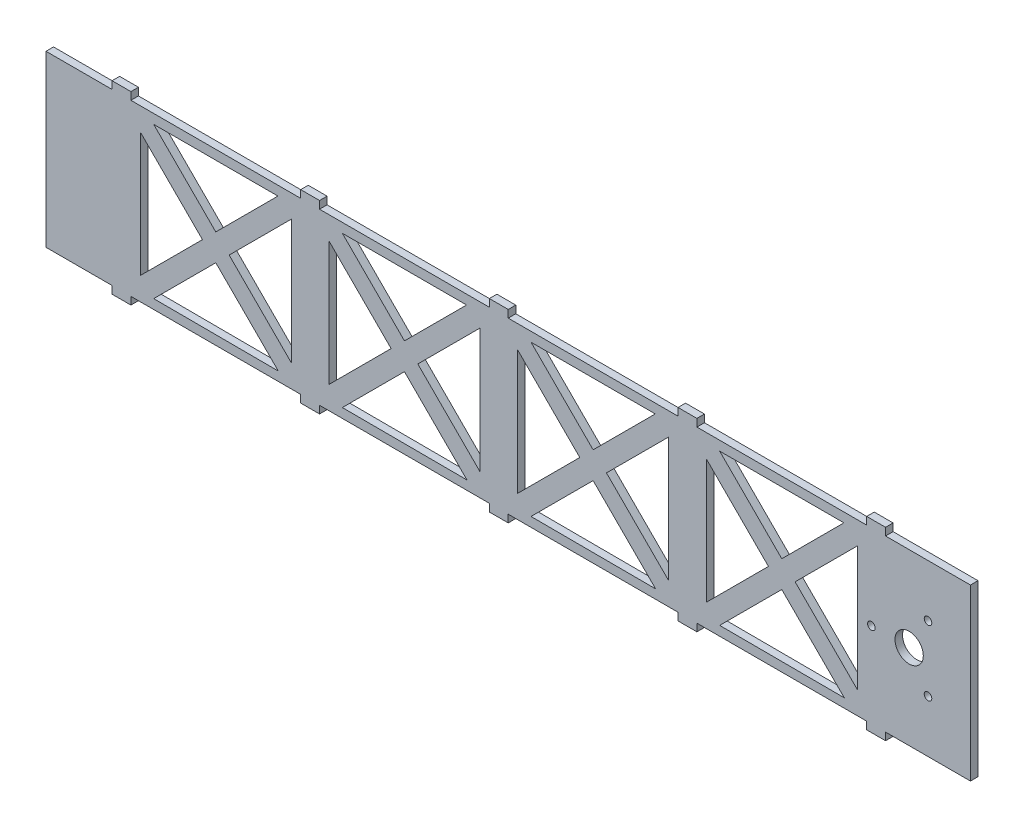
SolidWorks part; units mm, degrees
ref_plane "Piano frontale" through (0, 0, 0) normal (0, 0, 1) x (1, 0, 0)
ref_plane "Piano superiore" through (0, 0, 0) normal (0, 1, 0) x (1, 0, 0)
ref_plane "Piano destro" through (0, 0, 0) normal (1, 0, 0) x (0, 0, -1)
sketch "Schizzo1" plane through (0, 0, 0) normal (0, 0, 1) x (1, 0, 0)
  line L0 (0, 90) -> (0, 0)
  line L1 (0, 0) -> (35, 0)
  line L3 (0, 90) -> (35, 90)
  line L4 (490, 0) -> (490, 90)
  line L6 (490, 45) -> (0, 45) construction
  line L9 (45, 90) -> (45, 0) construction
  line L10 (135, 90) -> (135, 0) construction
  line L11 (45, 90) -> (135, 0) construction
  line L12 (45, 0) -> (135, 0) construction
  line L13 (135, 90) -> (45, 0) construction
  line L14 (50, 77.9289) -> (50, 12.0711)
  line L15 (130, 77.9289) -> (130, 12.0711)
  line L16 (45, 0) -> (50, 0) construction
  line L17 (50, 77.9289) -> (82.9289, 45)
  line L18 (57.0711, 85) -> (90, 52.0711)
  line L19 (122.9289, 85) -> (90, 52.0711)
  line L20 (130, 77.9289) -> (97.0711, 45)
  line L21 (57.0711, 85) -> (122.9289, 85)
  line L22 (123.1448, 4.7841) -> (57.0772, 5.0061)
  line L23 (131.4645, 93.5355) -> (41.4645, 3.5355) construction
  line L24 (138.5355, 86.4645) -> (48.5355, -3.5355) construction
  line L26 (41.4645, 86.4645) -> (131.4645, -3.5355) construction
  line L27 (130, 90) -> (130, 0) construction
  line L28 (48.5355, 93.5355) -> (138.5355, 3.5355) construction
  line L29 (90, 37.9289) -> (123.1448, 4.7841)
  line L30 (97.0711, 45) -> (130, 12.0711)
  line L31 (82.9289, 45) -> (50, 12.0711)
  line L32 (90, 37.9289) -> (57.0772, 5.0061)
  line L33 (150, 77.9289) -> (150, 12.0711)
  line L34 (230, 77.9289) -> (230, 12.0711)
  line L35 (150, 77.9289) -> (182.9289, 45)
  line L36 (157.0711, 85) -> (190, 52.0711)
  line L37 (222.9289, 85) -> (190, 52.0711)
  line L38 (230, 77.9289) -> (197.0711, 45)
  line L39 (157.0711, 85) -> (222.9289, 85)
  line L40 (223.1448, 4.7841) -> (157.0772, 5.0061)
  line L41 (190, 37.9289) -> (223.1448, 4.7841)
  line L42 (197.0711, 45) -> (230, 12.0711)
  line L43 (182.9289, 45) -> (150, 12.0711)
  line L44 (190, 37.9289) -> (157.0772, 5.0061)
  line L45 (445, 94) -> (445, 90)
  line L46 (250, 77.9289) -> (250, 12.0711)
  line L47 (330, 77.9289) -> (330, 12.0711)
  line L48 (250, 77.9289) -> (282.9289, 45)
  line L49 (257.0711, 85) -> (290, 52.0711)
  line L50 (322.9289, 85) -> (290, 52.0711)
  line L51 (330, 77.9289) -> (297.0711, 45)
  line L52 (257.0711, 85) -> (322.9289, 85)
  line L53 (323.1448, 4.7841) -> (257.0772, 5.0061)
  line L54 (290, 37.9289) -> (323.1448, 4.7841)
  line L55 (297.0711, 45) -> (330, 12.0711)
  line L56 (282.9289, 45) -> (250, 12.0711)
  line L57 (290, 37.9289) -> (257.0772, 5.0061)
  line L58 (350, 77.9289) -> (350, 12.0711)
  line L59 (430, 77.9289) -> (430, 12.0711)
  line L60 (350, 77.9289) -> (382.9289, 45)
  line L61 (357.0711, 85) -> (390, 52.0711)
  line L62 (422.9289, 85) -> (390, 52.0711)
  line L63 (430, 77.9289) -> (397.0711, 45)
  line L64 (435, 94) -> (445, 94)
  line L65 (357.0711, 85) -> (422.9289, 85)
  line L66 (423.1448, 4.7841) -> (357.0772, 5.0061)
  line L67 (390, 37.9289) -> (423.1448, 4.7841)
  line L68 (397.0711, 45) -> (430, 12.0711)
  line L69 (382.9289, 45) -> (350, 12.0711)
  line L70 (390, 37.9289) -> (357.0772, 5.0061)
  line L71 (50, 77.9289) -> (150, 77.9289) construction
  line L83 (435, 90) -> (435, 94)
  line L85 (35, 0) -> (35, -4)
  line L86 (35, -4) -> (45, -4)
  line L87 (45, -4) -> (45, 0)
  line L88 (135, 0) -> (135, -4)
  line L89 (135, -4) -> (145, -4)
  line L90 (145, -4) -> (145, 0)
  line L91 (235, 0) -> (235, -4)
  line L92 (235, -4) -> (245, -4)
  line L93 (245, -4) -> (245, 0)
  line L94 (335, 0) -> (335, -4)
  line L95 (335, -4) -> (345, -4)
  line L96 (345, -4) -> (345, 0)
  line L97 (435, 0) -> (435, -4)
  line L98 (435, -4) -> (445, -4)
  line L99 (445, -4) -> (445, 0)
  line L100 (445, 0) -> (490, 0)
  line L101 (345, 0) -> (435, 0)
  line L102 (245, 0) -> (335, 0)
  line L103 (145, 0) -> (235, 0)
  line L104 (45, 0) -> (135, 0)
  line L108 (345, 94) -> (345, 90)
  line L109 (335, 94) -> (345, 94)
  line L110 (335, 90) -> (335, 94)
  line L111 (245, 94) -> (245, 90)
  line L112 (235, 94) -> (245, 94)
  line L113 (235, 90) -> (235, 94)
  line L114 (145, 94) -> (145, 90)
  line L115 (135, 94) -> (145, 94)
  line L116 (135, 90) -> (135, 94)
  line L117 (45, 94) -> (45, 90)
  line L118 (35, 94) -> (45, 94)
  line L119 (35, 90) -> (35, 94)
  line L120 (45, 90) -> (135, 90)
  line L121 (145, 90) -> (235, 90)
  line L122 (245, 90) -> (335, 90)
  line L123 (345, 90) -> (435, 90)
  line L124 (445, 90) -> (490, 90)
  line L125 (467.5, 27.6795) -> (457.5, 45) construction
  line L126 (467.5, 62.3205) -> (457.5, 45) construction
  circle A0 centre (457.5, 45) radius 7.5
  circle A1 centre (437.5, 45) radius 2
  circle A2 centre (467.5, 27.6795) radius 2
  circle A3 centre (467.5, 62.3205) radius 2
  dimension "D19" = 15
  dimension "D20" = 4
  dimension "D22" = 4
  dimension "D2" = 490
  dimension "D3" = 35
  dimension "D6" = 5
  dimension "D8" = 5
  dimension "D9" = 5
  dimension "D10" = 5
  dimension "D11" = 32.5
  dimension "D13" = 10
  dimension "D14" = 5
  dimension "D15" = 4
  dimension "D16" = 4
  dimension "D17" = 4
  dimension "D18" = 4
  dimension "D21" = 20
  dimension "D23" = 20
  dimension "D24" = 4
  dimension "D25" = 100
  dimension "D26" = 4
extrude "Estrusione-Estrusione1" add sketch "Schizzo1" along normal blind 4
